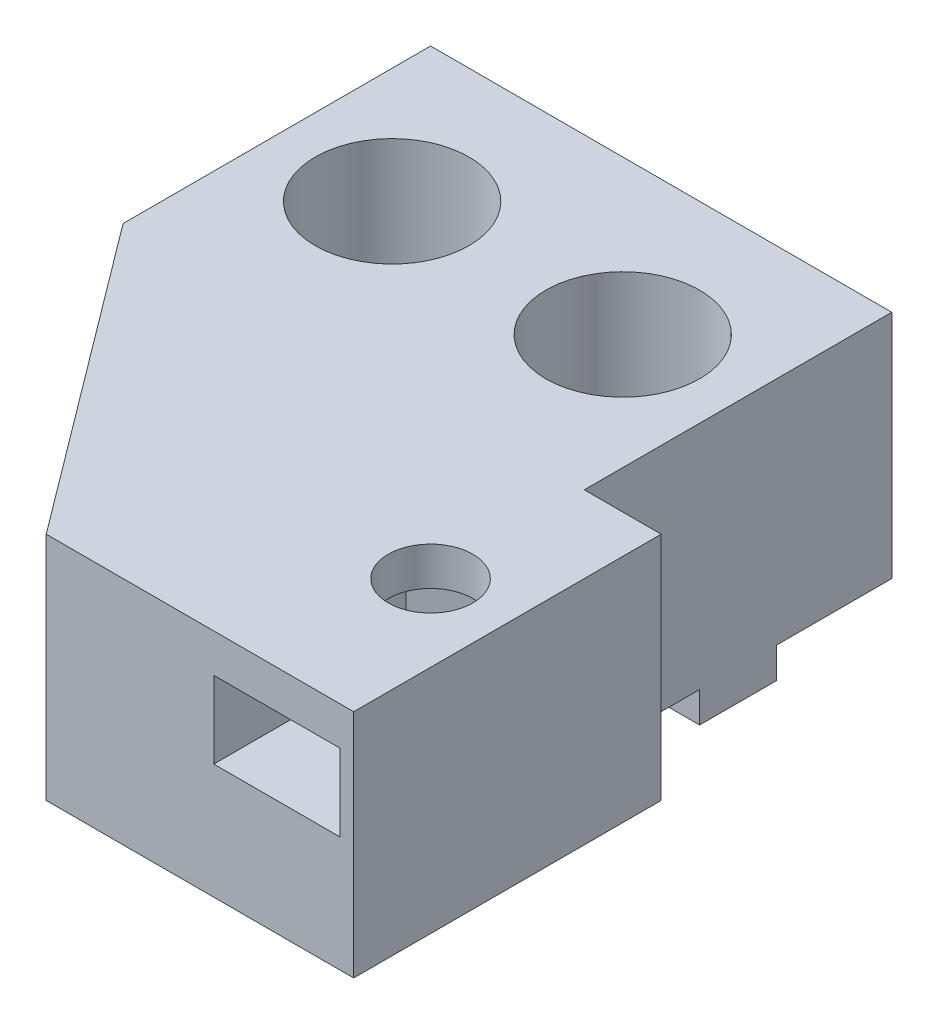
SolidWorks part; units mm, degrees
ref_plane "Front Plane" through (0, 0, 0) normal (0, 0, 1) x (1, 0, 0)
ref_plane "Top Plane" through (0, 0, 0) normal (0, 1, 0) x (1, 0, 0)
ref_plane "Right Plane" through (0, 0, 0) normal (1, 0, 0) x (0, 0, -1)
sketch "Sketch1" plane through (0, 0, 0) normal (0, 0, 1) x (1, 0, 0)
  line L1 (0, 0) -> (30, 0)
  line L2 (0, 0) -> (0, 15)
  line L3 (0, 15) -> (30, 15)
  line L4 (30, 0) -> (30, 15)
  dimension "D1" = 15
  dimension "D2" = 30
extrude "Boss-Extrude1" add sketch "Sketch1" along normal blind 20
sketch "Sketch2" plane through (0, 0, 20) normal (0, 0, 1) x (1, 0, 0)
  line L0 (30, 15) -> (0, 15) construction
  line L1 (0, 15) -> (0, 0) construction
  line L4 (10.9, 7.5) -> (19.1, 7.5)
  line L5 (10.9, 7.5) -> (10.9, 12.5)
  line L6 (10.9, 12.5) -> (19.1, 12.5)
  line L7 (19.1, 7.5) -> (19.1, 12.5)
  dimension "D7" = 5
  dimension "D8" = 8.2
  dimension "D9" = 10.9
  dimension "D10" = 2.5
extrude "Cut-Extrude1" cut sketch "Sketch2" against normal through all
sketch "Sketch3" plane through (0, 15, 0) normal (0, 1, 0) x (1, 0, 0)
  line L0 (0, -20) -> (0, 0) construction
  line L1 (30, 0) -> (0, 0) construction
  circle A0 centre (15, -10) radius 2.75
  dimension "D1" = 5.5
  dimension "D2" = 15
  dimension "D3" = 10
extrude "Cut-Extrude2" cut sketch "Sketch3" against normal through all
sketch "Sketch4" plane through (0, 7.5, 0) normal (0, 1, 0) x (1, 0, 0)
  line L0 (19.1, -7.5) -> (15.1, -5.1339)
  line L1 (19.1, 0) -> (19.1, -20) construction
  line L2 (15.1, -5.1339) -> (10.9, -7.5)
  line L3 (10.9, 0) -> (10.9, -20) construction
  line L8 (10.9, -20) -> (19.1, -20)
  line L9 (19.1, -20) -> (19.1, 0)
  line L10 (19.1, 0) -> (10.9, 0)
  line L11 (10.9, 0) -> (10.9, -20)
  line L13 (19.1, -7.5) -> (19.1, 0)
  line L14 (19.1, 0) -> (10.9, 0)
  line L15 (10.9, 0) -> (10.9, -7.5)
  point P4 (10.9, -10)
  point P9 (19.1, -10)
  dimension "D1" = 2.5
  dimension "D2" = 2.5
  dimension "D3" = 120
  dimension "D4" = 4
  dimension "D5" = 0
extrude "Boss-Extrude2" add sketch "Sketch4" along normal up to next
sketch "Sketch5" plane through (0, 0, 0) normal (0, 0, -1) x (-1, 0, 0)
  line L0 (-30, 15) -> (0, 15) construction
  line L1 (-15, 15) -> (15, 15)
  line L2 (-15, 15) -> (-15, 0)
  line L3 (-15, 0) -> (15, 0)
  line L4 (15, 15) -> (15, 0)
  dimension "D1" = 30
extrude "Boss-Extrude3" add sketch "Sketch5" along normal blind 20
sketch "Sketch6" plane through (0, 0, 0) normal (0, -1, 0) x (1, 0, 0)
  line L1 (15, -12.5) -> (-15, -12.5)
  line L2 (15, -12.5) -> (15, -7.5)
  line L3 (15, -7.5) -> (-15, -7.5)
  line L4 (-15, -12.5) -> (-15, -7.5)
  line L6 (15, -20) -> (-15, -20) construction
  line L8 (15, -20) -> (15, 0) construction
  line L9 (-15, -20) -> (-15, 0) construction
  dimension "D1" = 5
  dimension "D2" = 7.5
  dimension "D3" = 0
  dimension "D4" = 0
extrude "Boss-Extrude4" add sketch "Sketch6" along normal blind 2
sketch "Sketch7" plane through (0, 15, 0) normal (0, 1, 0) x (1, 0, 0)
  line L0 (-15, 20) -> (15, 20) construction
  line L1 (0, -20) -> (0, 0) construction
  line L2 (30, -20) -> (30, 0) construction
  circle A0 centre (7.5, 10) radius 2.75
  circle A1 centre (-7.5, 10) radius 2.75
  dimension "D1" = 5.5
  dimension "D2" = 5.5
  dimension "D4" = 10
  dimension "D6" = 37.5
  dimension "D3" = 10
  dimension "D5" = 7.5
extrude "Cut-Extrude3" cut sketch "Sketch7" against normal through all
sketch "Sketch8" plane through (0, 15, 0) normal (0, 1, 0) x (1, 0, 0)
  circle A0 centre (7.5, 10) radius 5
  circle A1 centre (-7.5, 10) radius 5
  dimension "D1" = 10
  dimension "D2" = 10
extrude "Cut-Extrude4" cut sketch "Sketch8" against normal offset from surface (10 mm away) 5 up to face at (15, 0, 12.75)
sketch "Sketch10" plane through (0, -2, 0) normal (0, -1, 0) x (1, 0, 0)
  circle A0 centre (-7.5, -10) radius 6
  circle A1 centre (7.5, -10) radius 6
  dimension "D1" = 12
  dimension "D2" = 12
extrude "Cut-Extrude5" cut sketch "Sketch10" against normal up to surface (2 mm away) up to face at (15, 0, 12.75)
sketch "Sketch11" plane through (0, 15, 0) normal (0, 1, 0) x (1, 0, 0)
  line L0 (-15, 0) -> (0, -20)
  line L1 (0, -20) -> (0, 0)
  line L2 (0, 0) -> (-15, 0)
extrude "Boss-Extrude5" add sketch "Sketch11" against normal up to surface (15 mm away) up to face at (0, 0, -10)
sketch "Sketch12" plane through (0, 15, 0) normal (0, 1, 0) x (1, 0, 0)
  line L0 (30, -20) -> (0, -20) construction
  line L1 (30, 0) -> (20, 0)
  line L2 (30, 0) -> (30, -20)
  line L3 (30, -20) -> (20, -20)
  line L4 (20, 0) -> (20, -20)
  dimension "D1" = 10
extrude "Cut-Extrude6" cut sketch "Sketch12" against normal up to surface (15 mm away) up to face at (0, 0, -10)
